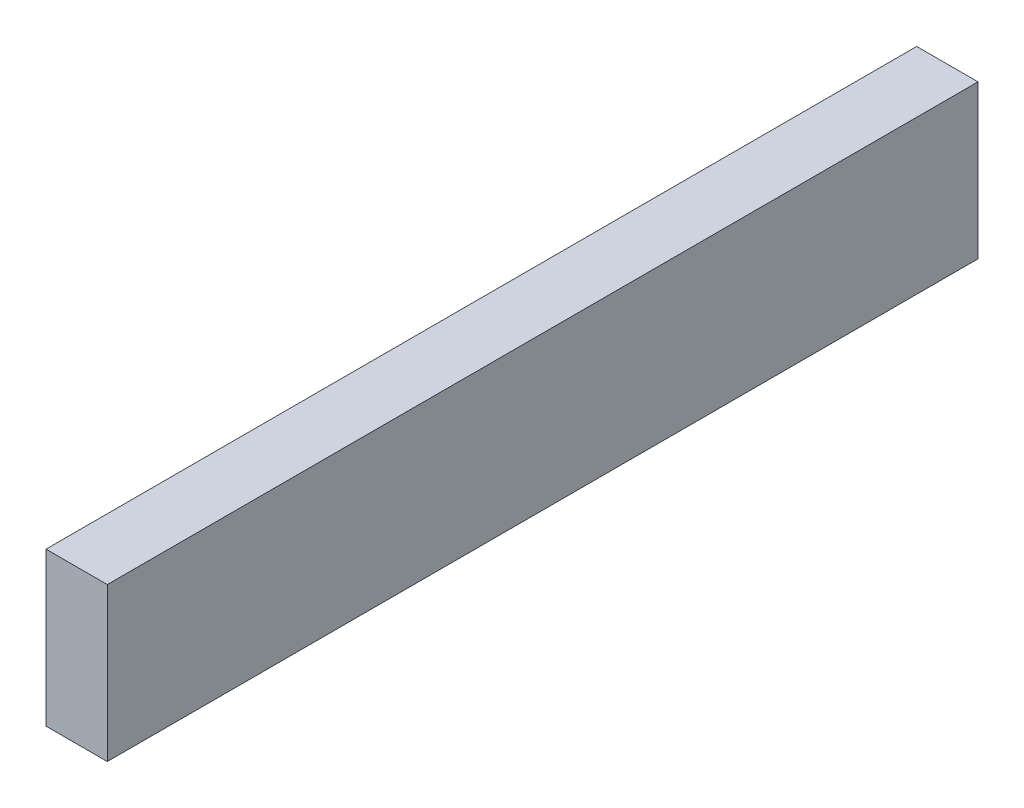
SolidWorks part; units mm, degrees
ref_plane "Front Plane" through (0, 0, 0) normal (0, 0, 1) x (1, 0, 0)
ref_plane "Top Plane" through (0, 0, 0) normal (0, 1, 0) x (1, 0, 0)
ref_plane "Right Plane" through (0, 0, 0) normal (1, 0, 0) x (0, 0, -1)
sketch "Sketch1" plane through (0, 0, 0) normal (0, 0, 1) x (1, 0, 0)
  line L1 (0, 0) -> (100, 0)
  line L2 (0, 0) -> (0, 250)
  line L3 (0, 250) -> (100, 250)
  line L4 (100, 0) -> (100, 250)
  dimension "D1" = 100
  dimension "D2" = 250
extrude "Boss-Extrude1" add sketch "Sketch1" along normal blind 1420
